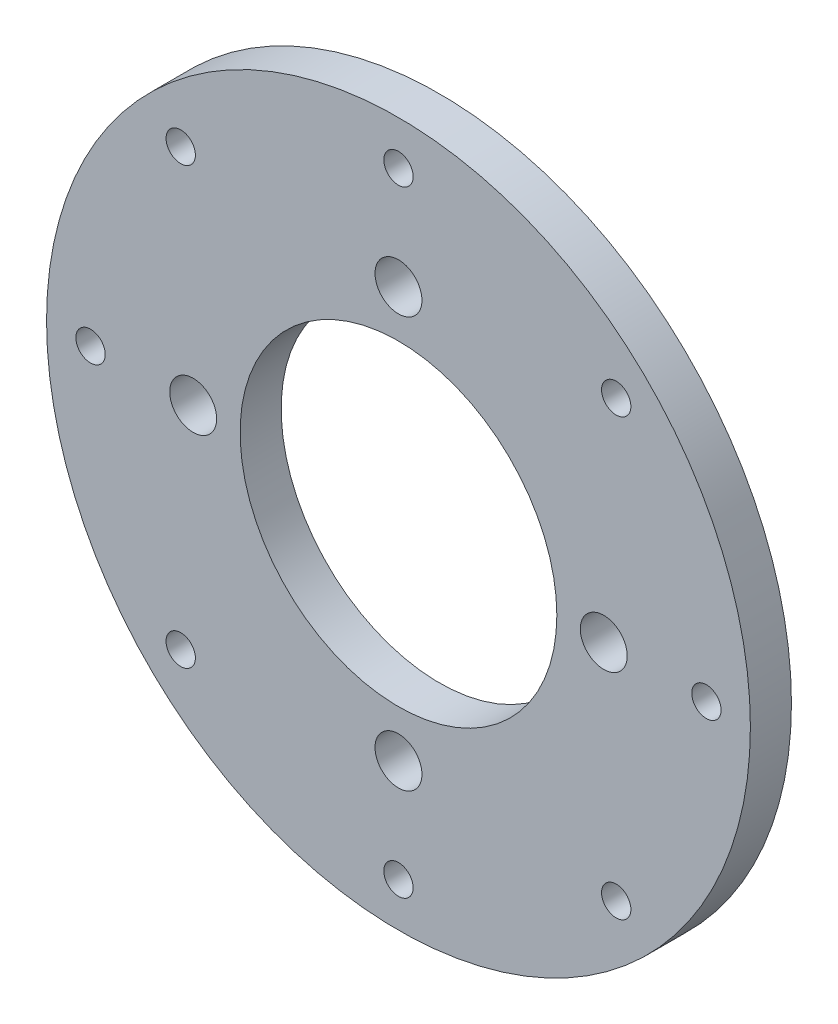
SolidWorks part; units mm, degrees
ref_plane "Alzado" through (0, 0, 0) normal (0, 0, 1) x (1, 0, 0)
ref_plane "Planta" through (0, 0, 0) normal (0, 1, 0) x (1, 0, 0)
ref_plane "Vista lateral" through (0, 0, 0) normal (1, 0, 0) x (0, 0, -1)
sketch "Croquis1" plane through (0, 0, 0) normal (0, 0, 1) x (1, 0, 0)
  circle A0 centre (0, 0) radius 60
  dimension "D1" = 120
extrude "Saliente-Extruir1" add sketch "Croquis1" along normal blind 7
sketch "Croquis2" plane through (0, 0, 7) normal (0, 0, 1) x (1, 0, 0)
  circle A0 centre (0, 0) radius 27
  dimension "D1" = 54
extrude "Cortar-Extruir1" cut sketch "Croquis2" against normal through all
sketch "Croquis3" plane through (0, 0, 7) normal (0, 0, 1) x (1, 0, 0)
  line L0 (60, 0) -> (-60, 0) construction
  line L1 (0, 60) -> (0, -60) construction
  circle A0 centre (0, 0) radius 60 construction
  circle A2 centre (0, 35) radius 4
  circle A3 centre (35, 0) radius 4
  circle A4 centre (0, -35) radius 4
  circle A5 centre (-35, 0) radius 4
  circle A6 centre (0, 0) radius 35 construction
  point P20 (0, 0)
  dimension "D1" = 70
  dimension "D3" = 8
  dimension "D2" = 4
extrude "Cortar-Extruir2" cut sketch "Croquis3" against normal through all
sketch "Croquis5" plane through (0, 0, 7) normal (0, 0, 1) x (1, 0, 0)
  circle A0 centre (0, 0) radius 52.5 construction
  circle A1 centre (0, 52.5) radius 2.5
  circle A2 centre (52.5, 0) radius 2.5
  circle A3 centre (0, -52.5) radius 2.5
  circle A4 centre (-52.5, 0) radius 2.5
  circle A5 centre (37.1231, 37.1231) radius 2.5
  circle A6 centre (52.5, 0) radius 2.5
  circle A7 centre (37.1231, -37.1231) radius 2.5
  circle A8 centre (0, -52.5) radius 2.5
  circle A9 centre (-37.1231, -37.1231) radius 2.5
  circle A10 centre (-52.5, 0) radius 2.5
  circle A11 centre (-37.1231, 37.1231) radius 2.5
  point P14 (0, 0)
  point P28 (0, 0)
  dimension "D1" = 105
  dimension "D2" = 5
  dimension "D4" = 8
  dimension "D3" = 4
extrude "Cortar-Extruir3" cut sketch "Croquis5" against normal through all contours A5 | A2 | A7 | A4 | A11 | A1 | A3 | A9
